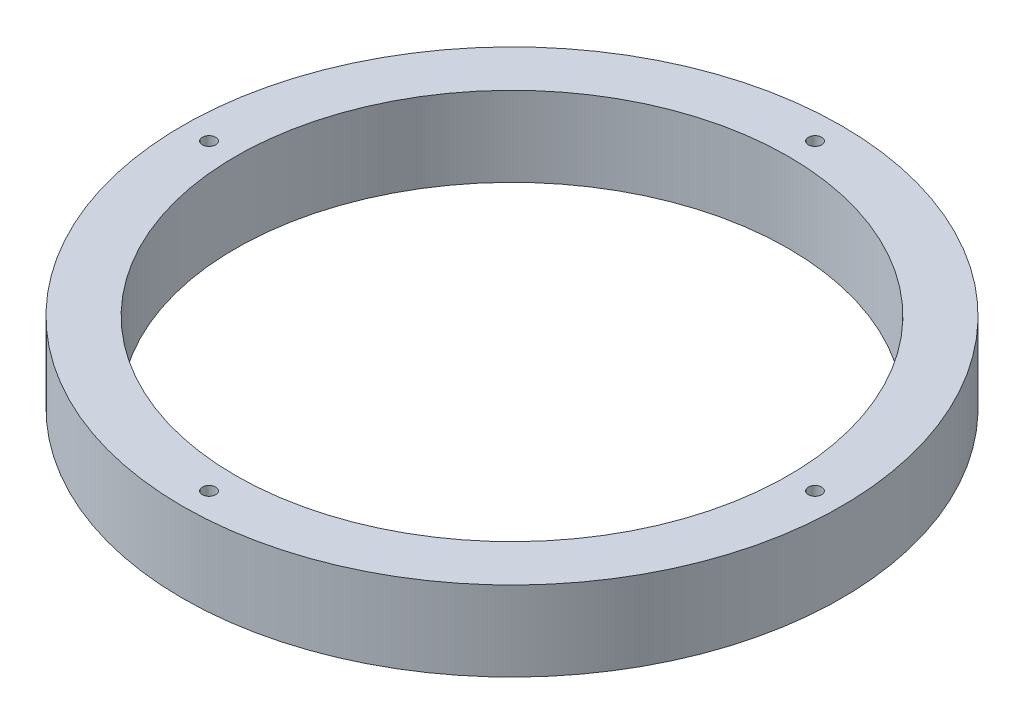
SolidWorks part; units mm, degrees
ref_plane "Front Plane" through (0, 0, 0) normal (0, 0, 1) x (1, 0, 0)
ref_plane "Top Plane" through (0, 0, 0) normal (0, 1, 0) x (1, 0, 0)
ref_plane "Right Plane" through (0, 0, 0) normal (1, 0, 0) x (0, 0, -1)
sketch "Sketch1" plane through (0, 0, 0) normal (0, 1, 0) x (1, 0, 0)
  line L0 (0, 36.195) -> (0, 0) construction
  circle A0 centre (0, 0) radius 33.02
  circle A1 centre (0, 0) radius 39.37
  circle A2 centre (0, 36.195) radius 0.7937
  circle A3 centre (36.195, 0) radius 0.7938
  circle A4 centre (0, -36.195) radius 0.7938
  circle A5 centre (-36.195, 0) radius 0.7938
  point P15 (0, 0)
  dimension "D1" = 66.04
  dimension "D2" = 78.74
  dimension "D4" = 1.5875
  dimension "D3" = 36.195
  dimension "D5" = 4
extrude "Boss-Extrude1" add sketch "Sketch1" along normal blind 9.525
